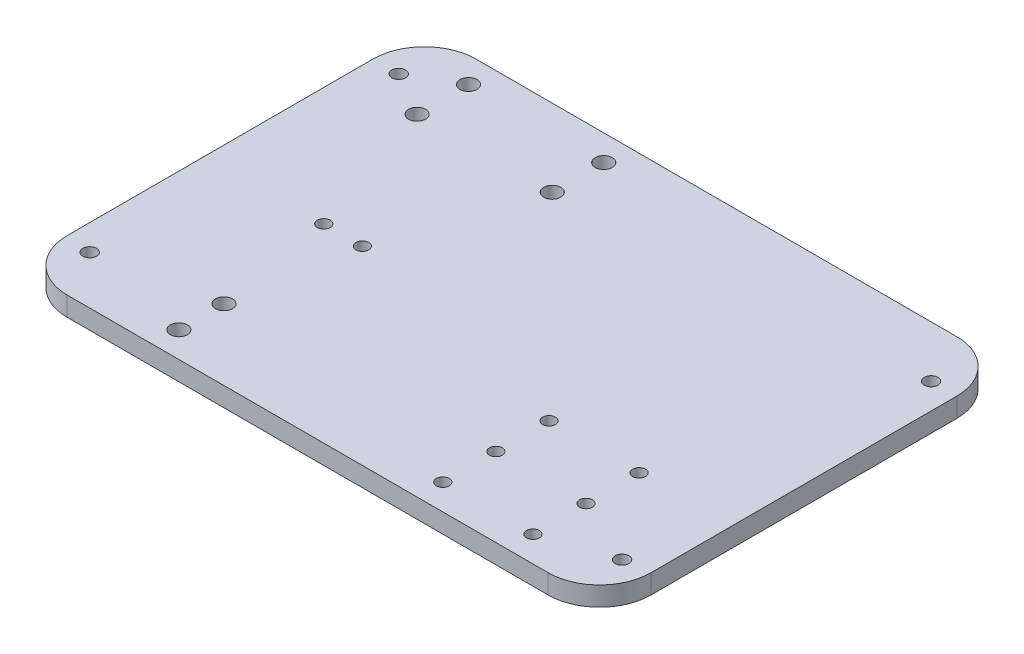
SolidWorks part; units mm, degrees
material "6061-T6 (SS)"
ref_plane "Front Plane" through (0, 0, 0) normal (0, 0, 1) x (1, 0, 0)
ref_plane "Top Plane" through (0, 0, 0) normal (0, 1, 0) x (1, 0, 0)
ref_plane "Right Plane" through (0, 0, 0) normal (1, 0, 0) x (0, 0, -1)
sketch "Sketch1" plane through (0, 0, 0) normal (0, 1, 0) x (1, 0, 0)
  line L1 (-143.999, -100.8062) -> (143.9989, -100.8062)
  line L2 (-143.999, -100.8062) -> (-143.999, 100.8063)
  line L3 (-143.999, 100.8063) -> (143.9989, 100.8063)
  line L4 (143.9989, -100.8062) -> (143.9989, 100.8063)
  line L5 (-143.999, -100.8062) -> (143.9989, 100.8063) construction
  line L6 (-143.999, 100.8063) -> (143.9989, -100.8062) construction
  point P0 (0, 0)
  dimension "D1" = 287.9979
  dimension "D2" = 201.6125
extrude "Boss-Extrude1" add sketch "Sketch1" along normal blind 9.525
fillet "Fillet2" radius 25.4 4 edges at (-143.999, 4.7625, -100.8063) (143.9989, 4.7625, -100.8063) (143.9989, 4.7625, 100.8062) (-143.999, 4.7625, 100.8062)
sketch "Sketch2" plane through (0, 0, 0) normal (0, 1, 0) x (1, 0, 0)
  line L0 (143.9989, -75.4062) -> (143.9989, 75.4063) construction
  line L5 (118.5989, 100.8063) -> (-118.599, 100.8063) construction
  line L6 (-143.999, -100.8062) -> (143.9989, -100.8062)
  line L8 (-143.999, -100.8062) -> (-143.999, 100.8063)
  line L13 (-143.999, 100.8063) -> (143.9989, 100.8063)
  line L14 (143.9989, -100.8062) -> (143.9989, 100.8063)
  line L15 (-118.599, -100.8062) -> (118.5989, -100.8062) construction
  line L17 (-131.299, -76.9937) -> (131.2989, -76.9937)
  line L18 (-131.299, -76.9937) -> (-131.299, 75.4063)
  line L19 (-131.299, 75.4063) -> (131.2989, 75.4063)
  line L20 (131.2989, -76.9937) -> (131.2989, 75.4063)
  line L23 (-143.999, 75.4062) -> (-143.999, -75.4062) construction
  point P0 (0, 0)
  point P5 (139.4731, 100.8063)
  point P6 (-36.0911, 20.8609)
  dimension "D1" = 25.4
  dimension "D2" = 12.7
  dimension "D3" = 152.4
  dimension "D4" = 12.7
hole_wizard "1/4 Clearance Hole1" positions "Sketch3" profile "Sketch4" hole size "1/4" standard "ANSI Inch"
sketch "Sketch3" plane through (0, 9.525, 0) normal (0, 1, 0) x (1, 0, 0)
  point P12 (-131.299, 75.4063)
  point P15 (131.2989, 75.4063)
  point P18 (131.2989, -76.9937)
  point P21 (-131.299, -76.9937)
sketch "Sketch4" plane through (-131.299, 9.525, -75.4063) normal (1, 0, 0) x (0, 0, 1)
  line L0 (0, 0) -> (0, 23.6198)
  line L1 (0, 23.6198) -> (3.3782, 21.59)
  line L2 (3.3782, 21.59) -> (3.3782, 0)
  line L5 (3.3782, 0) -> (0, 0)
  line L10 (0, 23.6198) -> (-3.3782, 21.59) construction
  line L11 (0, -6.35) -> (0, 107.95) construction
  dimension "Hole Dia." = 6.7564
  dimension "Hole Depth" = 21.59
  dimension "Drill Angle" = 118
sketch "Sketch9" plane through (0, 0, 0) normal (0, 1, 0) x (1, 0, 0)
  line L0 (-76.2, 0) -> (76.2, 0) construction
  line L1 (76.2, 0) -> (76.2, -61.9125) construction
  line L2 (-76.2, -76.9938) -> (-76.2, 75.4063) construction
  line L3 (-95.25, -7.1437) -> (-85.725, -7.1437) construction
  line L16 (-76.2, -65.8813) -> (-76.2, -88.1063) construction
  line L17 (-118.599, -100.8062) -> (118.5989, -100.8062) construction
  line L22 (-109.5426, 88.1063) -> (-109.5426, 62.7063) construction
  line L23 (-42.8574, 62.7063) -> (-42.8574, 88.1063) construction
  line L24 (93.6625, -96.8375) -> (103.1875, -96.8375)
  line L25 (-109.5426, 75.4063) -> (-42.8574, 75.4063) construction
  line L31 (98.425, -88.1063) -> (98.425, -35.7188) construction
  line L32 (53.975, -88.1063) -> (53.975, -35.7188) construction
  line L33 (76.2, -61.9125) -> (53.975, -61.9125) construction
  line L35 (76.2, -61.9125) -> (98.425, -61.9125) construction
  line L36 (93.6625, -96.8375) -> (93.6625, -26.9875)
  line L37 (93.6625, -26.9875) -> (103.1875, -26.9875)
  line L38 (103.1875, -96.8375) -> (103.1875, -26.9875)
  line L39 (93.6625, -96.8375) -> (103.1875, -26.9875) construction
  line L40 (93.6625, -26.9875) -> (103.1875, -96.8375) construction
  line L41 (49.2125, -96.8375) -> (58.7375, -96.8375)
  line L42 (49.2125, -96.8375) -> (49.2125, -26.9875)
  line L43 (49.2125, -26.9875) -> (58.7375, -26.9875)
  line L44 (58.7375, -96.8375) -> (58.7375, -26.9875)
  line L45 (49.2125, -96.8375) -> (58.7375, -26.9875) construction
  line L46 (49.2125, -26.9875) -> (58.7375, -96.8375) construction
  line L51 (-95.25, -21.4312) -> (-57.15, -21.4312)
  line L52 (-95.25, -21.4312) -> (-95.25, 7.1438)
  line L57 (-95.25, 7.1438) -> (-57.15, 7.1438)
  line L58 (-57.15, -21.4312) -> (-57.15, 7.1438)
  line L59 (-95.25, -100.8063) -> (-57.15, -100.8063)
  line L60 (-95.25, -100.8063) -> (-95.25, -53.1812)
  line L61 (-95.25, -53.1812) -> (-57.15, -53.1812)
  line L62 (-57.15, -100.8063) -> (-57.15, -53.1812)
  line L63 (-95.25, -100.8063) -> (-57.15, -53.1812) construction
  line L64 (-95.25, -53.1812) -> (-57.15, -100.8063) construction
  line L65 (-95.25, -21.4312) -> (-57.15, 7.1438) construction
  line L66 (-95.25, 7.1438) -> (-57.15, -21.4312) construction
  line L67 (-95.25, -27.7812) -> (-57.15, -27.7812)
  line L68 (-95.25, -27.7812) -> (-95.25, -21.4312)
  line L69 (-95.25, -21.4312) -> (-57.15, -21.4312)
  line L70 (-57.15, -27.7812) -> (-57.15, -21.4312)
  line L71 (-95.25, -27.7812) -> (-57.15, -21.4312) construction
  line L72 (-95.25, -21.4312) -> (-57.15, -27.7812) construction
  line L73 (-85.725, -7.1437) -> (-76.2, -7.1437) construction
  line L74 (-76.2, -7.1437) -> (-66.675, -7.1437) construction
  line L75 (-66.675, -7.1437) -> (-57.15, -7.1437) construction
  point P4 (0, 0)
  point P34 (-109.5426, 75.4063)
  point P42 (53.975, -61.9125)
  point P43 (98.425, -61.9125)
  point P51 (-76.2, -7.1437)
  point P56 (-76.2, -24.6062)
  dimension "D1" = 152.4
  dimension "D7" = 66.6852
  dimension "D8" = 25.4
  dimension "D10" = 152.4
  dimension "D3" = 22.225
  dimension "D4" = 12.7
  dimension "D9" = 52.3875
  dimension "D2" = 12.7
  dimension "D5" = 9.525
  dimension "D6" = 8.7312
  dimension "D11" = 34.925
  dimension "D14" = 38.1
  dimension "D12" = 25.4
  dimension "D13" = 6.35
  dimension "D15" = 28.575
hole_wizard "5/16 Clearance Hole1" positions "Sketch14" profile "Sketch15" hole size "5/16" standard "ANSI Inch" end condition through all
sketch "Sketch14" plane through (0, 0, 0) normal (0, -1, 0) x (-1, 0, 0)
  point P0 (76.2, -88.1063)
  point P6 (76.2, -65.8813)
  point P12 (42.8574, 88.1063)
  point P15 (109.5426, 62.7063)
  point P18 (42.8574, 62.7063)
  point P21 (109.5426, 88.1063)
sketch "Sketch15" plane through (-76.2, 0, 88.1063) normal (1, 0, 0) x (0, 0, -1)
  line L0 (0, 0) -> (0, 9.525)
  line L1 (0, 9.525) -> (4.2164, 9.525)
  line L2 (4.2164, 9.525) -> (4.2164, 0)
  line L5 (4.2164, 0) -> (0, 0)
  line L11 (0, -6.35) -> (0, 107.95) construction
  dimension "Thru Hole Dia." = 8.4328
  dimension "Thru Hole Depth" = 9.525
hole_wizard "1/4 (0.25) Diameter Hole2" positions "Sketch10" profile "Sketch11" hole size "1/4" standard "ANSI Inch"
sketch "Sketch10" plane through (0, 9.525, 0) normal (0, 1, 0) x (1, 0, 0)
  line L0 (53.975, -88.1063) -> (53.975, -35.7188) construction
  point P36 (53.975, -35.7188)
  point P39 (98.425, -35.7188)
  point P42 (98.425, -61.9125)
  point P45 (98.425, -88.1063)
  point P48 (53.975, -88.1063)
  point P51 (53.975, -61.9125)
  point P55 (-66.675, -7.1437)
  point P58 (-85.725, -7.1437)
sketch "Sketch11" plane through (53.975, 9.525, 35.7188) normal (1, 0, 0) x (0, 0, 1)
  line L0 (0, 0) -> (0, 23.4977)
  line L1 (0, 23.4977) -> (3.175, 21.59)
  line L2 (3.175, 21.59) -> (3.175, 0)
  line L5 (3.175, 0) -> (0, 0)
  line L10 (0, 23.4977) -> (-3.175, 21.59) construction
  line L11 (0, -6.35) -> (0, 107.95) construction
  dimension "Hole Dia." = 6.35
  dimension "Hole Depth" = 21.59
  dimension "Drill Angle" = 118
sketch "Sketch16" [suppressed] plane through (0, 9.525, 0) normal (0, 1, 0) x (1, 0, 0)
  line L0 (-133.35, -120.65) -> (133.35, -120.65) construction
  line L1 (-99.3775, -57.15) -> (-53.0225, -57.15) construction
  line L2 (-99.3775, -57.15) -> (-99.3775, -120.65) construction
  line L3 (-99.3775, -120.65) -> (-53.0225, -120.65)
  line L4 (-53.0225, -57.15) -> (-53.0225, -120.65) construction
  line L5 (-99.3775, -57.15) -> (-53.0225, -120.65) construction
  line L6 (-99.3775, -120.65) -> (-53.0225, -57.15) construction
  line L7 (-76.2, -82.55) -> (-76.2, -104.775) construction
  line L8 (76.2, -63.5) -> (76.2, -101.6) construction
  line L9 (-109.5426, 71.4375) -> (-109.5426, 46.0375) construction
  line L10 (50.6413, -57.15) -> (101.7588, -57.15)
  line L11 (50.6413, -57.15) -> (50.6413, -120.65)
  line L12 (50.6413, -120.65) -> (101.7588, -120.65)
  line L13 (101.7588, -57.15) -> (101.7588, -120.65)
  line L14 (50.6413, -57.15) -> (101.7588, -120.65) construction
  line L15 (50.6413, -120.65) -> (101.7588, -57.15) construction
  line L16 (-42.8574, 71.4375) -> (-42.8574, 46.0375) construction
  line L17 (-132.7201, 84.1375) -> (-137.1328, 85.3725)
  line L18 (-132.7201, 84.1375) -> (-86.3651, 84.1375)
  line L19 (-132.7201, 84.1375) -> (-132.7201, 33.3375)
  line L20 (-132.7201, 33.3375) -> (-86.3651, 33.3375)
  line L21 (-86.3651, 84.1375) -> (-86.3651, 33.3375)
  line L22 (-132.7201, 84.1375) -> (-86.3651, 33.3375) construction
  line L23 (-132.7201, 33.3375) -> (-86.3651, 84.1375) construction
  line L24 (-66.0349, 84.1375) -> (-19.6799, 84.1375)
  line L25 (-66.0349, 84.1375) -> (-66.0349, 33.3375)
  line L26 (-66.0349, 33.3375) -> (-19.6799, 33.3375)
  line L27 (-19.6799, 84.1375) -> (-19.6799, 33.3375)
  line L28 (-66.0349, 84.1375) -> (-19.6799, 33.3375) construction
  line L29 (-66.0349, 33.3375) -> (-19.6799, 84.1375) construction
  line L30 (-86.3651, 84.1375) -> (-66.0349, 84.1375)
  line L31 (-19.6799, 84.1375) -> (139.6051, 85.7245)
  line L32 (149.225, 76.2) -> (149.225, -101.6)
  line L33 (101.7588, -120.65) -> (141.9552, -110.8542)
  line L34 (50.6413, -120.65) -> (-53.0225, -120.65)
  line L35 (-99.3775, -120.65) -> (-141.8355, -110.8825)
  line L36 (-149.225, 76.2) -> (-149.225, -101.6)
  line L37 (-109.5426, 58.7375) -> (-76.2, -88.9) construction
  line L38 (-76.2, -88.9) -> (-42.8574, 58.7375) construction
  line L39 (-42.8574, 58.7375) -> (-109.5426, 58.7375) construction
  line L40 (76.2, -88.9) -> (139.7, -101.6) construction
  line L41 (139.7, 76.2) -> (76.2, -88.9) construction
  line L42 (-42.8574, 58.7375) -> (139.7, -101.6) construction
  line L43 (-76.2, -88.9) -> (139.7, 76.2) construction
  line L44 (-14.3453, 46.3729) -> (27.9886, 9.1916)
  line L45 (36.0363, 8.9186) -> (96.0438, 54.8066)
  line L46 (92.1232, 66.2005) -> (-10.2182, 65.1808)
  line L47 (-16.5049, 58.8311) -> (-16.5049, 51.144)
  line L48 (52.6489, -2.3593) -> (100.8579, 34.5064)
  line L49 (110.642, 27.1827) -> (87.8701, -32.0241)
  line L50 (77.753, -34.5157) -> (52.3158, -12.1746)
  line L51 (-19.6799, 33.3375) -> (-53.0225, -57.15)
  line L52 (-132.7201, 33.3375) -> (-99.3775, -57.15)
  line L53 (-32.3679, -28.6447) -> (-17.3343, 12.1547)
  line L54 (-7.1855, 14.7302) -> (10.6497, -0.9342)
  line L55 (10.3166, -10.7494) -> (-22.5522, -35.8844)
  line L56 (-53.0225, -57.15) -> (50.6413, -57.15) construction
  line L57 (117.8983, -7.0181) -> (101.4445, -49.798)
  line L58 (103.1808, -56.8486) -> (119.6346, -71.2997)
  line L59 (130.175, -66.5286) -> (130.175, -9.2976)
  line L60 (76.2, -88.9) -> (31.4827, -6.5544) construction
  line L61 (8.3554, -36.2308) -> (22.5295, -25.3918)
  line L62 (31.9671, -27.4056) -> (37.8531, -38.2447)
  line L63 (32.2728, -47.625) -> (12.2127, -47.625)
  line L64 (133.35, 120.65) -> (-133.35, 120.65) construction
  line L65 (-158.75, 120.65) -> (158.75, 120.65)
  line L66 (-158.75, 120.65) -> (-158.75, -120.65)
  line L67 (-158.75, -120.65) -> (158.75, -120.65)
  line L68 (158.75, 120.65) -> (158.75, -120.65)
  line L69 (-158.75, 95.25) -> (-158.75, -95.25) construction
  line L71 (158.75, -95.25) -> (158.75, 95.25) construction
  circle A0 centre (-139.7, 76.2) radius 9.525
  circle A1 centre (-139.7, -101.6) radius 9.525
  circle A2 centre (139.7, 76.2) radius 9.525
  circle A3 centre (139.7, -101.6) radius 9.525
  circle A4 centre (-109.5426, 71.4375) radius 4.2164 construction
  circle A5 centre (-109.5426, 46.0375) radius 4.2164 construction
  arc A6 (96.0438, 54.8066) -> (92.1232, 66.2005) centre (92.1865, 59.8508) ccw
  arc A7 (27.9886, 9.1916) -> (36.0363, 8.9186) centre (32.179, 13.9627) ccw
  arc A8 (-14.3453, 46.3729) -> (-16.5049, 51.144) centre (-10.1549, 51.144) cw
  arc A9 (-10.2182, 65.1808) -> (-16.5049, 58.8311) centre (-10.1549, 58.8311) ccw
  arc A10 (87.8701, -32.0241) -> (77.753, -34.5157) centre (81.9434, -29.7446) cw
  arc A11 (100.8579, 34.5064) -> (110.642, 27.1827) centre (104.7152, 29.4622) cw
  arc A12 (52.6489, -2.3593) -> (52.3158, -12.1746) centre (56.5062, -7.4035) ccw
  arc A13 (-32.3679, -28.6447) -> (-22.5522, -35.8844) centre (-26.4095, -30.8402) ccw
  arc A14 (10.6497, -0.9342) -> (10.3166, -10.7494) centre (6.4593, -5.7052) cw
  arc A15 (-17.3343, 12.1547) -> (-7.1855, 14.7302) centre (-11.3759, 9.9592) cw
  arc A16 (119.6346, -71.2997) -> (130.175, -66.5286) centre (123.825, -66.5286) ccw
  arc A17 (101.4445, -49.798) -> (103.1808, -56.8486) centre (107.3712, -52.0775) ccw
  arc A18 (117.8983, -7.0181) -> (130.175, -9.2976) centre (123.825, -9.2976) cw
  arc A19 (8.3554, -36.2308) -> (12.2127, -47.625) centre (12.2127, -41.275) ccw
  arc A20 (37.8531, -38.2447) -> (32.2728, -47.625) centre (32.2728, -41.275) cw
  arc A21 (22.5295, -25.3918) -> (31.9671, -27.4056) centre (26.3868, -30.436) cw
  circle A22 centre (-42.8574, 71.4375) radius 4.2164 construction
  circle A23 centre (-76.2, -82.55) radius 4.2164 construction
  circle A24 centre (-76.2, -104.775) radius 4.2164 construction
  point P16 (-76.2, -88.9)
  point P28 (76.2, -82.55)
  point P44 (-109.5426, 58.7375)
  point P49 (-42.8574, 58.7375)
  point P50 (-109.5426, 58.7375)
  point P51 (-42.8574, 58.7375)
  point P116 (0, 0)
  line M10 (133.35, 120.65) -> (-133.35, 120.65)
  arc M11 (-133.35, 120.65) -> (-158.75, 95.25) centre (-133.35, 95.25) ccw
  line M12 (-158.75, 95.25) -> (-158.75, -95.25)
  arc M13 (-158.75, -95.25) -> (-133.35, -120.65) centre (-133.35, -95.25) ccw
  line M14 (-133.35, -120.65) -> (133.35, -120.65)
  arc M15 (133.35, -120.65) -> (158.75, -95.25) centre (133.35, -95.25) ccw
  line M16 (158.75, -95.25) -> (158.75, 95.25)
  arc M17 (158.75, 95.25) -> (133.35, 120.65) centre (133.35, 95.25) ccw
  dimension "D1" = 19.05
  dimension "D12" = 6.35
  dimension "D17" = 6.35
  dimension "D21" = 6.35
  dimension "D25" = 6.35
  dimension "D29" = 6.35
  dimension "D2" = 46.355
  dimension "D3" = 63.5
  dimension "D4" = 51.1175
  dimension "D5" = 63.5
  dimension "D6" = 46.355
  dimension "D7" = 50.8
  dimension "D9" = 9.525
  dimension "D10" = 19.05
  dimension "D11" = 3.175
  dimension "D8" = 9.525
  dimension "D13" = 9.525
  dimension "D14" = 9.525
  dimension "D15" = 9.525
  dimension "D16" = 152.4
  dimension "D18" = 9.525
  dimension "D19" = 9.525
  dimension "D20" = 9.525
  dimension "D22" = 19.05
  dimension "D23" = 9.525
  dimension "D24" = 9.525
  dimension "D26" = 9.525
  dimension "D27" = 9.525
  dimension "D28" = 9.525
extrude "Cut-Extrude1" [suppressed] cut sketch "Sketch16" against normal through all contours A3 L33 L35 A1 L36 A0 L17 L18 L30 L24 L31 A2 L32 M14 M15 M16 M17 M10 M11 M12 M13 | A15 L53 A13 L55 A14 L54 | L46 A9 L47 A8 L44 A7 L45 A6 | L48 A12 L50 A10 L49 A11 | A18 L57 A17 L58 A16 L59 | A21 L61 A19 L63 A20 L62
sketch "Sketch8" plane through (0, 0, 0) normal (0, 1, 0) x (1, 0, 0)
  line L1 (17.7944, 74.1465) -> (93.9944, 74.1465)
  line L2 (17.7944, 74.1465) -> (17.7944, -52.8535)
  line L3 (17.7944, -52.8535) -> (93.9944, -52.8535)
  line L4 (93.9944, 74.1465) -> (93.9944, -52.8535)
  line L5 (17.7944, 74.1465) -> (93.9944, -52.8535) construction
  line L6 (17.7944, -52.8535) -> (93.9944, 74.1465) construction
  point P0 (55.8944, 10.6465)
  dimension "D1" = 127
  dimension "D2" = 76.2
fillet "Fillet3" [suppressed] radius 6.35
equation "\"master cylinder spacing\"= 66.68515647mm"
equation "\"master cylinder mounting hole spacing\"= 1in"
equation "\"D8@Sketch9\"=\"master cylinder mounting hole spacing\""
equation "\"D7@Sketch9\"=\"master cylinder spacing\""
equation "\"accelerator pedal mount hole spacing\"= 1.5in"
equation "\"brake pedal mount hole spacing\"= 7 / 8in"
equation "\"D3@Sketch9\"=\"brake pedal mount hole spacing\""
equation "\"D2@Sketch16\"=1.625in+0.1+.1"
equation "\"D4@Sketch16\"=1.8125in+.1+.1"
equation "\"D6@Sketch16\"=1.625in+.1+.1"
equation "\"brake pedal space from edge\"= 1 / 2in"
equation "\"accelerator pedal space from edge\"= .75in"
equation "\"D4@Sketch9\"=\"brake pedal space from edge\""
equation "\"new accelerator pedal mount hole spacing\"= 52.38750000mm"
equation "\"D9@Sketch9\"=\"new accelerator pedal mount hole spacing\""
equation "\"D11@Sketch9\"=1.375in"
equation "\"BOTS mount length\"= 1 + 1 / 8in"
equation "\"BOTS mount wall thickness\"= 1 / 4in"
equation "\"BOTS mount to brake pedal mount space\"= 1in"
equation "\"D12@Sketch9\"=\"BOTS mount to brake pedal mount space\""
equation "\"D13@Sketch9\"=\"BOTS mount wall thickness\""
equation "\"D15@Sketch9\"=\"BOTS mount length\""
